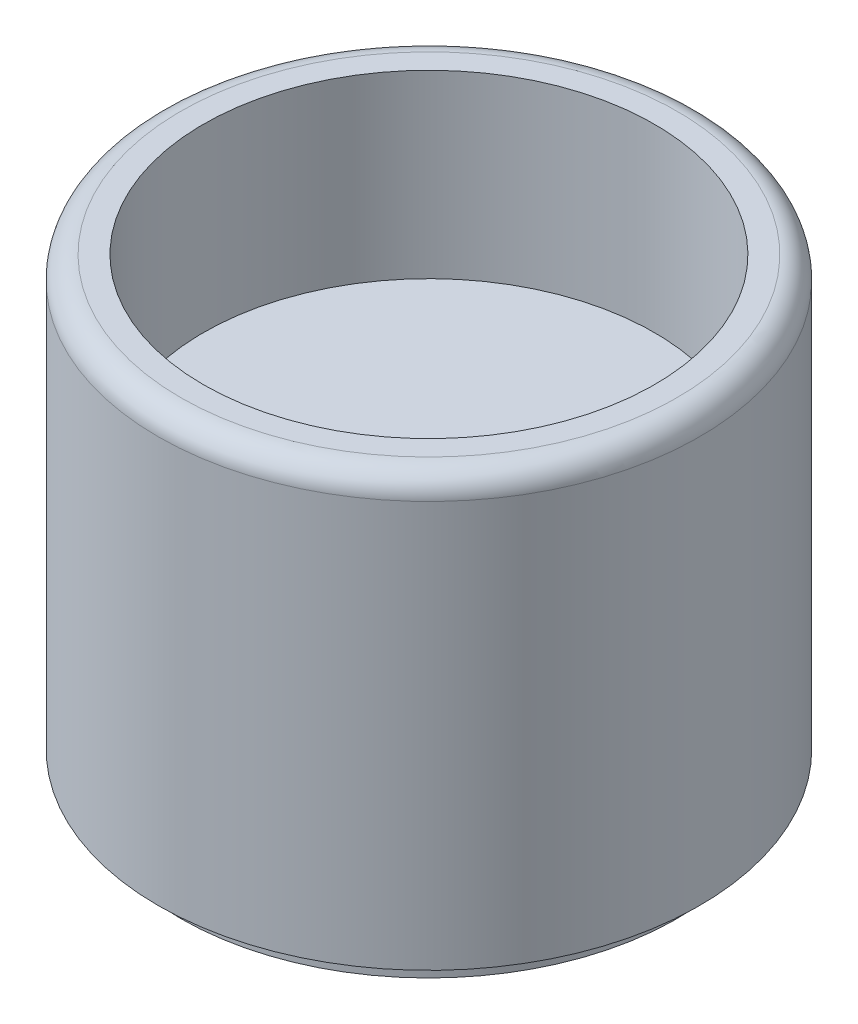
SolidWorks part; units mm, degrees
ref_plane "Front Plane" through (0, 0, 0) normal (0, 0, 1) x (1, 0, 0)
ref_plane "Top Plane" through (0, 0, 0) normal (0, 1, 0) x (1, 0, 0)
ref_plane "Right Plane" through (0, 0, 0) normal (1, 0, 0) x (0, 0, -1)
sketch "Sketch1" plane through (0, 0, 0) normal (0, 1, 0) x (1, 0, 0)
  circle A0 centre (0, 0) radius 6
extrude "Boss-Extrude1" add sketch "Sketch1" along normal blind 10
fillet "Fillet1" radius 0.5 1 edges at (0, 10, 6)
sketch "Sketch2" plane through (0, 0, 0) normal (0, 1, 0) x (1, 0, 0)
  circle A0 centre (0, 0) radius 5.5
extrude "Cut-Extrude11" cut sketch "Sketch2" along normal blind 0.5 flip side to cut
sketch "Sketch3" plane through (0, 10, 0) normal (0, 1, 0) x (1, 0, 0)
  circle A0 centre (0, 0) radius 5
extrude "Cut-Extrude12" cut sketch "Sketch3" against normal blind 4
